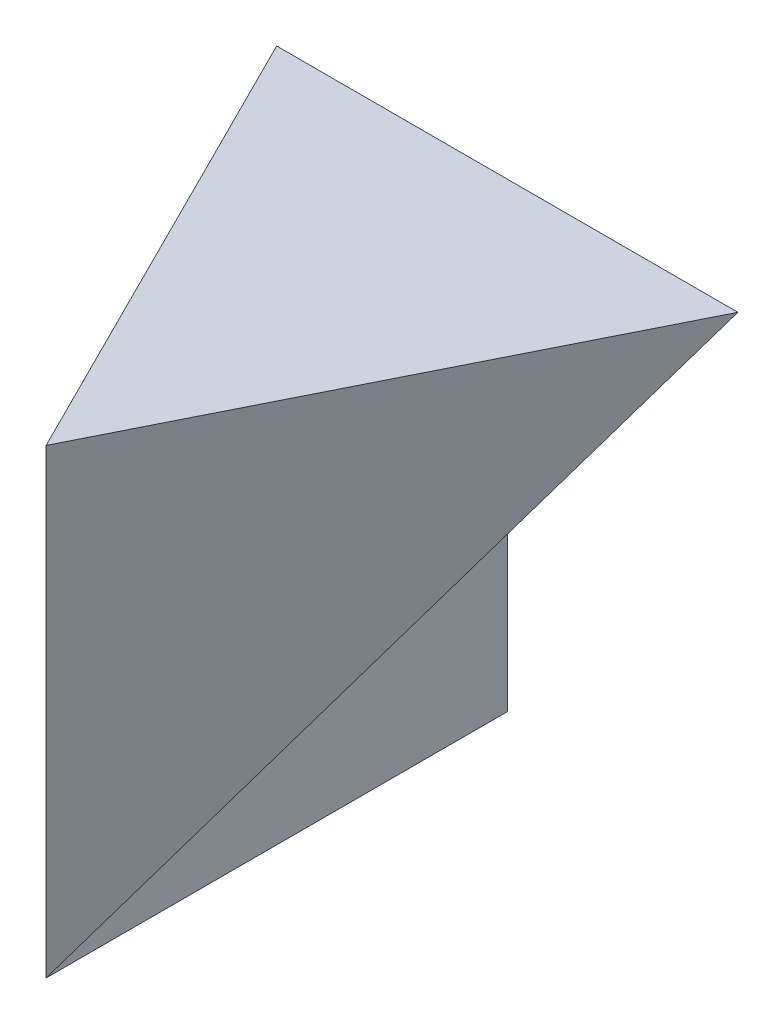
SolidWorks part; units mm, degrees
ref_plane "Front Plane" through (0, 0, 0) normal (0, 0, 1) x (1, 0, 0)
ref_plane "Top Plane" through (0, 0, 0) normal (0, 1, 0) x (1, 0, 0)
ref_plane "Right Plane" through (0, 0, 0) normal (1, 0, 0) x (0, 0, -1)
sketch "Sketch1" plane through (0, 0, 0) normal (1, 0, 0) x (0, 0, -1)
  line L1 (0, 0) -> (40, 0)
  line L2 (0, 0) -> (0, 40)
  line L3 (0, 40) -> (40, 40)
  line L4 (40, 0) -> (40, 40)
  dimension "D1" = 40
  dimension "D2" = 40
extrude "Boss-Extrude1" add sketch "Sketch1" along normal blind 40
sketch "Sketch2" plane through (40, 0, 0) normal (1, 0, 0) x (0, 0, -1)
  line L0 (0, 0) -> (40, 40)
  line L1 (40, 40) -> (40, 0)
  line L2 (40, 0) -> (0, 0)
extrude "Cut-Extrude1" cut sketch "Sketch2" against normal blind 20
sketch "Sketch3" plane through (0, 0, 0) normal (0, 0, 1) x (1, 0, 0)
  line L0 (20, 0) -> (40, 40)
  line L1 (40, 40) -> (40, 0)
  line L2 (40, 0) -> (0, 0)
  line L3 (0, 0) -> (0, 40)
  line L4 (0, 40) -> (20, 0)
extrude "Cut-Extrude2" cut sketch "Sketch3" against normal blind 60 contours L4 L3 L2 | L2 L1 L0
sketch "Sketch4" plane through (0, 0, 0) normal (0, 1, 0) x (1, 0, 0)
  line L0 (20, 0) -> (40, 40)
  line L1 (40, 40) -> (40, 0)
  line L2 (40, 0) -> (0, 0)
  line L3 (0, 0) -> (0, 40)
  line L4 (0, 40) -> (20, 0)
extrude "Cut-Extrude3" cut sketch "Sketch4" along normal blind 60 contours L4 L3 L2 | L2 L1 L0
